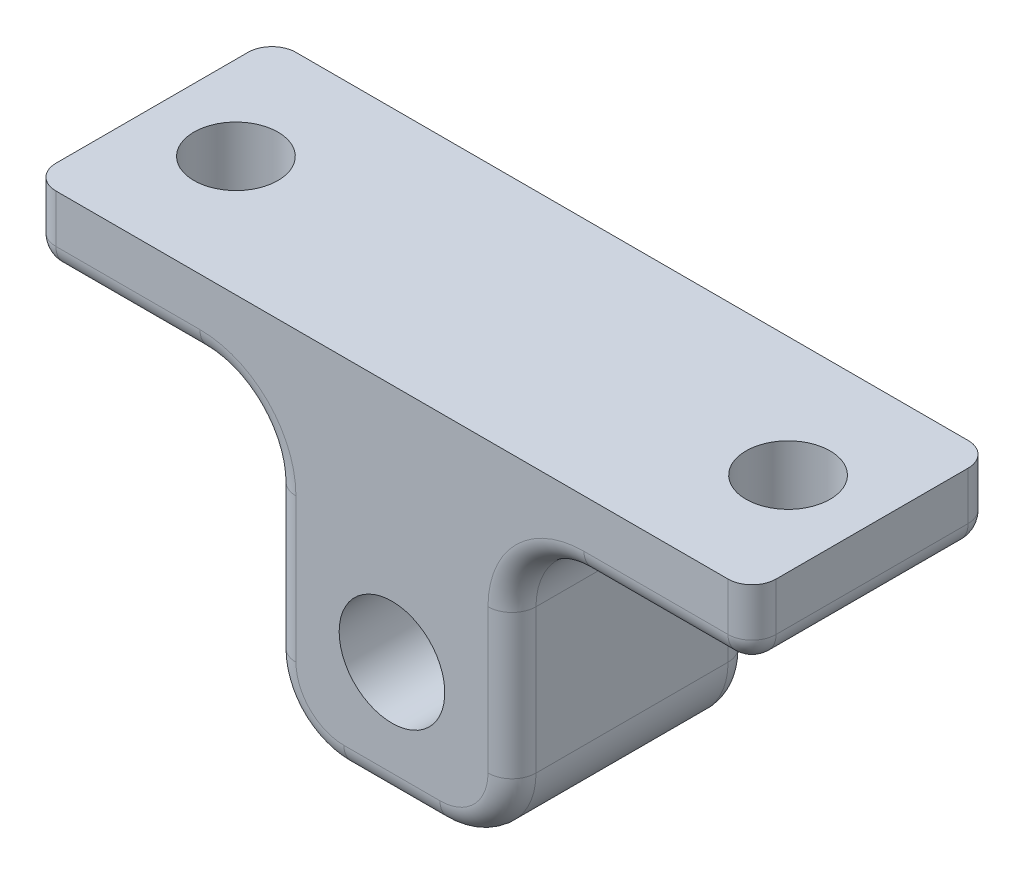
SolidWorks part; units mm, degrees
ref_plane "正面" through (0, 0, 0) normal (0, 0, 1) x (1, 0, 0)
ref_plane "平面" through (0, 0, 0) normal (0, 1, 0) x (1, 0, 0)
ref_plane "右側面" through (0, 0, 0) normal (1, 0, 0) x (0, 0, -1)
sketch "ｽｹｯﾁ1" plane through (0, 0, 0) normal (0, 0, 1) x (1, 0, 0)
  line L0 (0, 10) -> (0, -5)
  line L1 (5, -5) -> (-5, -5)
  line L2 (5, -5) -> (5, 10)
  line L3 (5, 10) -> (-5, 10)
  line L4 (-5, -5) -> (-5, 10)
  line L5 (5, 10) -> (15, 10)
  line L6 (5, 10) -> (5, 7)
  line L7 (5, 7) -> (15, 7)
  line L8 (15, 10) -> (15, 7)
  line L9 (-15, 10) -> (-15, 7)
  line L10 (-5, 7) -> (-15, 7)
  line L11 (-5, 10) -> (-5, 7)
  line L12 (-5, 10) -> (-15, 10)
  line L13 (5, -5) -> (5, 10)
  line L14 (-5, -5) -> (-5, 10)
  line L15 (5, 10) -> (15, 10)
  line L16 (15, 10) -> (5, 10)
  dimension "D1" = 15
  dimension "D2" = 10
  dimension "D5" = 3
  dimension "D6" = 10
extrude "ﾎﾞｽ - 押し出し1" add sketch "ｽｹｯﾁ1" along normal blind 10 contours L2 L3 L0 L1 | L8 L5 L2 L7 | L4 L1 L0 L3 | L4 L12 L9 L10
sketch "ｽｹｯﾁ2" plane through (0, 0, 0) normal (0, 0, -1) x (-1, 0, 0)
  line L0 (-5, -5) -> (5, -5) construction
  circle A0 centre (0, 0) radius 2.2
  dimension "D1" = 4.4
extrude "ｶｯﾄ - 押し出し1" cut sketch "ｽｹｯﾁ2" against normal through all
sketch "ｽｹｯﾁ3" plane through (0, 7, 0) normal (0, -1, 0) x (1, 0, 0)
  line L0 (-15, 10) -> (-15, 0) construction
  line L1 (-5, 0) -> (-15, 0) construction
  line L2 (0, 0.3201) -> (0, 10.158)
  circle A0 centre (-11.5, 5) radius 1.75
  circle A1 centre (11.5, 5) radius 1.75
  dimension "D1" = 3.5
  dimension "D2" = 3.5
  dimension "D3" = 5
extrude "ｶｯﾄ - 押し出し2" cut sketch "ｽｹｯﾁ3" against normal through all contours A0 | A1
fillet "ﾌｨﾚｯﾄ1" radius 3 4 edges at (-5, 7, 5) (5, 7, 5) (-5, -5, 5) (5, -5, 5)
fillet "ﾌｨﾚｯﾄ2" radius 1 24 edges at (11.5, 7, 10) (11.5, 7, 0) (5.8787, 6.1213, 10) (5.8787, 6.1213, 0) (5, 1, 0) (5, 1, 10) (4.1213, -4.1213, 10) (4.1213, -4.1213, 0) (0, -5, 10) (0, -5, 0) (-4.1213, -4.1213, 10) (-4.1213, -4.1213, 0) (-5, 1, 10) (-5, 1, 0) (-5.8787, 6.1213, 10) (-5.8787, 6.1213, 0) (-15, 8.5, 0) (-15, 8.5, 10) (15, 8.5, 0) (15, 8.5, 10) (15, 7, 5) (-11.5, 7, 0) (-11.5, 7, 10) (-15, 7, 5)
